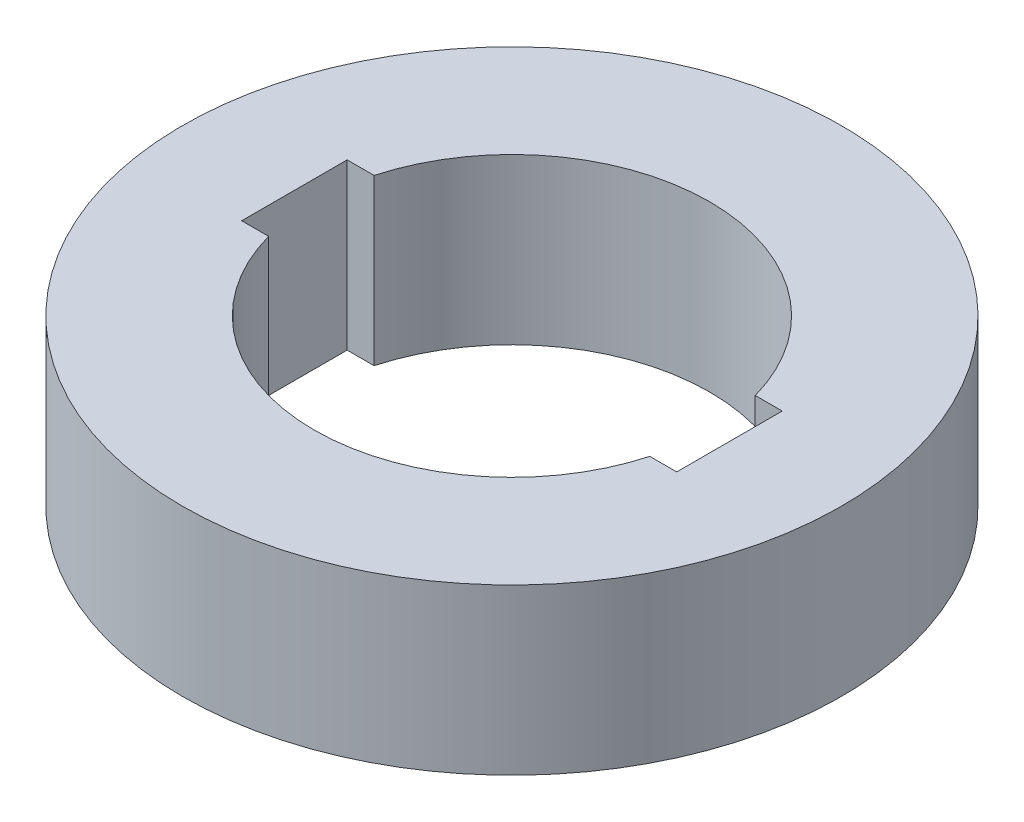
SolidWorks part; units mm, degrees
ref_plane "Front Plane" through (0, 0, 0) normal (0, 0, 1) x (1, 0, 0)
ref_plane "Top Plane" through (0, 0, 0) normal (0, 1, 0) x (1, 0, 0)
ref_plane "Right Plane" through (0, 0, 0) normal (1, 0, 0) x (0, 0, -1)
sketch "Sketch1" plane through (0, 0, 0) normal (0, 1, 0) x (1, 0, 0)
  line L1 (-33, -8) -> (33, -8)
  line L2 (-33, -8) -> (-33, 8)
  line L3 (-33, 8) -> (33, 8)
  line L4 (33, -8) -> (33, 8)
  line L5 (-33, -8) -> (33, 8) construction
  line L6 (-33, 8) -> (33, -8) construction
  circle A0 centre (0, 0) radius 50
  circle A1 centre (0, 0) radius 30
  dimension "D1" = 100
  dimension "D2" = 60
  dimension "D3" = 66
  dimension "D4" = 16
extrude "Boss-Extrude1" add sketch "Sketch1" along normal blind 25 contours A0 A1 L3 L4 L1 L2
